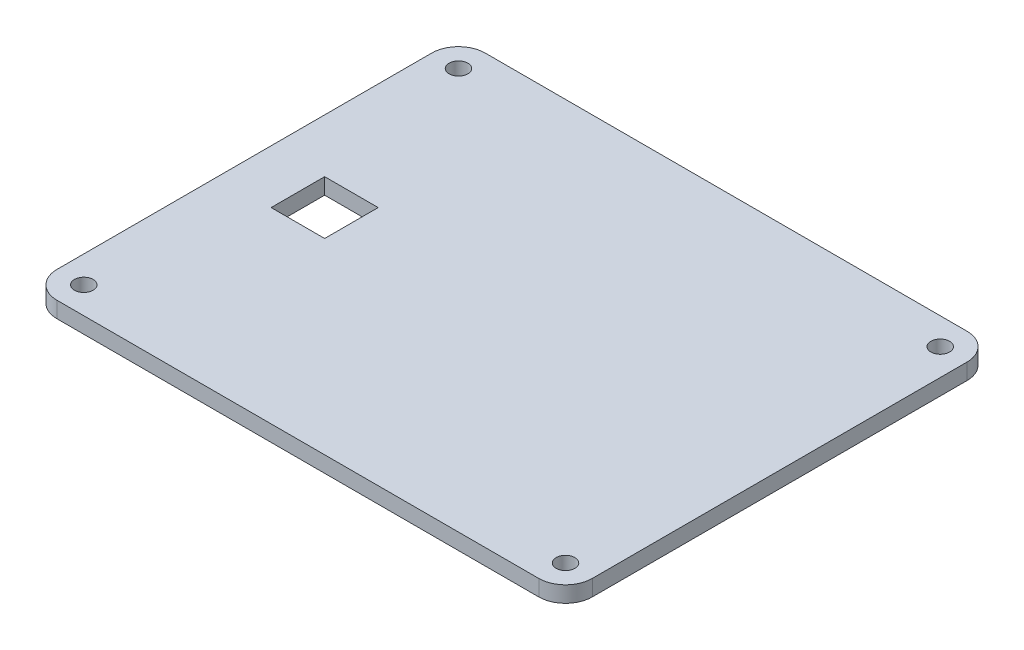
SolidWorks part; units mm, degrees
ref_plane "Front Plane" through (0, 0, 0) normal (0, 0, 1) x (1, 0, 0)
ref_plane "Top Plane" through (0, 0, 0) normal (0, 1, 0) x (1, 0, 0)
ref_plane "Right Plane" through (0, 0, 0) normal (1, 0, 0) x (0, 0, -1)
sketch "Sketch1" plane through (0, 0, 0) normal (0, 1, 0) x (1, 0, 0)
  line L1 (-45, 40) -> (45, 40)
  line L2 (-50, 35) -> (-50, -35)
  line L3 (-45, -40) -> (45, -40)
  line L4 (50, 35) -> (50, -35)
  line L5 (-50, 40) -> (50, -40) construction
  line L6 (-50, -40) -> (50, 40) construction
  arc A0 (45, 40) -> (50, 35) centre (45, 35) cw
  arc A1 (45, -40) -> (50, -35) centre (45, -35) ccw
  arc A2 (-50, -35) -> (-45, -40) centre (-45, -35) ccw
  arc A3 (-45, 40) -> (-50, 35) centre (-45, 35) ccw
  point P0 (0, 0)
  dimension "D3" = 5
  dimension "D1" = 100
  dimension "D2" = 80
extrude "Boss-Extrude1" add sketch "Sketch1" along normal blind 3
sketch "Sketch3" plane through (0, 3, 0) normal (0, 1, 0) x (1, 0, 0)
  line L0 (-45, -40) -> (45, -40) construction
  line L1 (-50, 35) -> (-50, -35) construction
  circle A0 centre (-45, -35) radius 1.75
  dimension "D1" = 3.5
  dimension "D2" = 5
  dimension "D3" = 5
extrude "Cut-Extrude2" cut sketch "Sketch3" against normal through all
pattern_linear "LPattern1" count 2 spacing 70 along (0, 0, -1) count 2 spacing 90 along (1, 0, 0) of "Cut-Extrude2"
sketch "Sketch5" plane through (0, 3, 0) normal (0, 1, 0) x (1, 0, 0)
  line L0 (-50, 35) -> (-50, -35) construction
  line L5 (-40, 5) -> (-30, 5)
  line L6 (-40, 5) -> (-40, -5)
  line L7 (-40, -5) -> (-30, -5)
  line L8 (-30, 5) -> (-30, -5)
  line L9 (-40, 5) -> (-30, -5) construction
  line L10 (-40, -5) -> (-30, 5) construction
  line L11 (-45, -40) -> (45, -40) construction
  point P0 (-35, 0)
  dimension "D1" = 10
  dimension "D2" = 10
  dimension "D3" = 10
  dimension "D4" = 35
extrude "Cut-Extrude4" cut sketch "Sketch5" against normal through all
